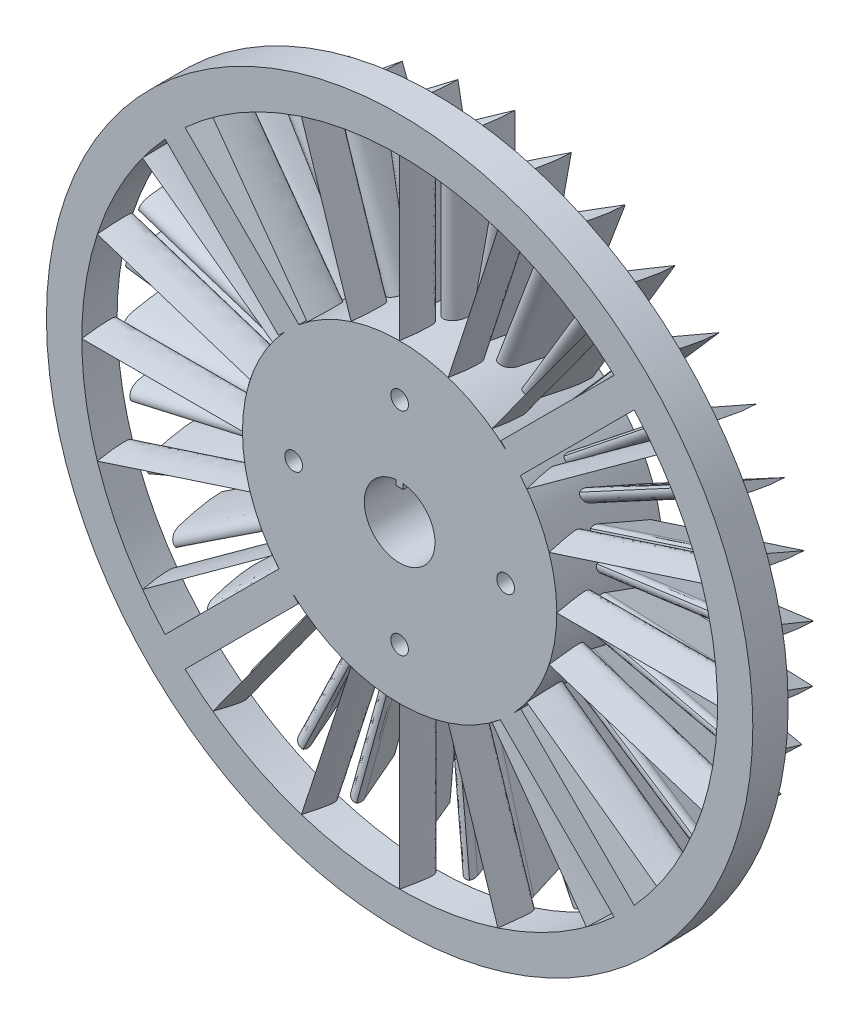
SolidWorks part; units mm, degrees
ref_plane "Front Plane" through (0, 0, 0) normal (0, 0, 1) x (1, 0, 0)
ref_plane "Top Plane" through (0, 0, 0) normal (0, 1, 0) x (1, 0, 0)
ref_plane "Right Plane" through (0, 0, 0) normal (1, 0, 0) x (0, 0, -1)
sketch "Sketch6" plane through (0, 0, 0) normal (0, 0, 1) x (1, 0, 0)
  circle A0 centre (0, 0) radius 5
  circle A1 centre (0, 0) radius 22.25
  dimension "D1" = 44.5
  dimension "D2" = 10
extrude "Boss-Extrude3" add sketch "Sketch6" along normal blind 5
sketch "Sketch7" plane through (0, 0, 0) normal (0, 0, 1) x (1, 0, 0)
  circle A0 centre (0, 0) radius 45
  circle A1 centre (0, 0) radius 50
  dimension "D1" = 100
  dimension "D2" = 90
extrude "Boss-Extrude4" add sketch "Sketch7" along normal blind 5 separate body
sketch "Sketch8" plane through (0, 0, 0) normal (0, 0, 1) x (1, 0, 0)
  line L0 (0, 0) -> (50, 0) construction
  line L1 (0, 0) -> (35.3553, 35.3553) construction
  line L2 (14.4153, 17.2437) -> (30.3741, 33.2026)
  line L3 (17.2434, 14.415) -> (33.2026, 30.3741)
  line L4 (14.4153, 17.2437) -> (14.3184, 17.1468)
  line L5 (17.2434, 14.415) -> (16.9587, 14.1302)
  circle A0 centre (0, 0) radius 50 construction
  circle A1 centre (0, 0) radius 45 construction
  arc A3 (30.3741, 33.2026) -> (33.2026, 30.3741) centre (0, 0) cw
  arc A6 (14.3184, 17.1468) -> (16.9587, 14.1302) centre (-2.7185, -0.4287) cw
  dimension "D1" = 45
  dimension "D3" = 4
extrude "Boss-Extrude6" add sketch "Sketch8" along normal blind 5 contours L2 A3 L3 L5 A6 L4
pattern_circular "CirPattern1" count 4 over 360 about axis through (0, 0, 0) along (0, 0, 1) of "Boss-Extrude6"
ref_plane "Plane3" through (0, 22.21, 0) normal (0, 1, 0) x (1, 0, 0)
sketch "Sketch14" plane through (0, 22.21, 0) normal (0, 1, 0) x (1, 0, 0)
  spline S0 degree 3 poles (0, 0) (-0.3698, -0.0668) (-0.7189, -0.6282) (-0.5661, -2.4228) (-0.2391, -3.8029) (0, -4.9965) knots 0 0 0 0 0.192523 0.324416 1 1 1 1
  spline S1 degree 3 poles (0, 0) (0.031, -0.0068) (0.1382, -0.0513) (0.3359, -0.3357) (0.3645, -0.7871) (0.362, -1.3706) (0.3351, -1.9913) (0.2952, -2.6334) (0.2039, -3.6437) (0.1081, -4.4063) (0, -4.9965) knots 0 0 0 0 0.018561 0.066312 0.190216 0.274897 0.408433 0.551848 0.650333 1 1 1 1
extrude "Boss-Extrude9" add sketch "Sketch14" along normal blind 24 contours S1 S0
pattern_circular "CirPattern4" count 20 over 360 of "Boss-Extrude9"
sketch "Sketch16" plane through (0, 0, 5) normal (0, 0, 1) x (1, 0, 0)
  circle A0 centre (0, 0) radius 15 construction
  circle A1 centre (0, 15) radius 1.25
  circle A2 centre (-15, 0) radius 1.25
  circle A3 centre (0, -15) radius 1.25
  circle A4 centre (15, 0) radius 1.25
  dimension "D1" = 30
  dimension "D2" = 2.5
extrude "Cut-Extrude1" cut sketch "Sketch16" against normal through all
sketch "Sketch23" plane through (0, 0, 0) normal (0, 0, -1) x (-1, 0, 0)
  circle A0 centre (0, 0) radius 22.25
  circle A1 centre (0, 0) radius 5
  dimension "D1" = 10
extrude "Boss-Extrude11" add sketch "Sketch23" along normal blind 10
sketch "Sketch25" plane through (0, 0, 0) normal (0, 0, -1) x (-1, 0, 0)
  circle A0 centre (15, 0) radius 1.25 construction
  circle A1 centre (0, -15) radius 1.25 construction
  circle A2 centre (-15, 0) radius 1.25 construction
  circle A3 centre (0, 15) radius 1.25 construction
  circle A4 centre (15, 0) radius 1.25
  circle A5 centre (0, -15) radius 1.25
  circle A6 centre (-15, 0) radius 1.25
  circle A7 centre (0, 15) radius 1.25
extrude "Cut-Extrude2" cut sketch "Sketch25" along normal through all
ref_plane "Plane4" through (0, 18, 0) normal (0, 1, 0) x (1, 0, 0)
sketch "Sketch26" plane through (0, 18, 0) normal (0, 1, 0) x (1, 0, 0)
  line L0 (0, 0) -> (0, 0.864) construction
  line L1 (2.9925, 10) -> (2.5911, 8.7315) construction
  line L2 (5, 10) -> (-5, 10) construction
  line L3 (0, 2.0079) -> (2.5911, 8.7315)
  spline S0 degree 3 poles (0, 0.864) (0.4836, 0.6154) (1.2939, 1.0595) (1.7163, 2.0284) (1.8829, 2.8557) (2.0402, 3.7765) (2.202, 4.7015) (2.3311, 5.6673) (2.5317, 6.9834) (2.5546, 8.0221) (2.5911, 8.7315) knots 0 0 0 0 0.164115 0.250545 0.34698 0.442301 0.559859 0.657473 0.76469 1 1 1 1
  spline S1 degree 2 poles (0, 0.864) (-0.2705, 1.4222) (0, 2.0079) knots 0 0 0 1 1 1
extrude "Boss-Extrude12" add sketch "Sketch26" along normal up to surface (27 mm away)
pattern_circular "CirPattern5" count 35 over 360 about axis through (0, 0, -10) along (0, 0, -1) of "Boss-Extrude12"
sketch "Sketch27" plane through (0, 0, -10) normal (0, 0, -1) x (-1, 0, 0)
  line L0 (0, 0) -> (0, 5) construction
  line L2 (-0.5, 5.75) -> (0.5, 5.75)
  line L3 (-0.5, 5.75) -> (-0.5, 4.25)
  line L4 (-0.5, 4.25) -> (0.5, 4.25)
  line L5 (0.5, 5.75) -> (0.5, 4.25)
  line L6 (-0.5, 5.75) -> (0.5, 4.25) construction
  line L7 (-0.5, 4.25) -> (0.5, 5.75) construction
  circle A0 centre (0, 0) radius 5 construction
  dimension "D1" = 1.5
  dimension "D2" = 1
extrude "Boss-Extrude13" add sketch "Sketch27" against normal through all
